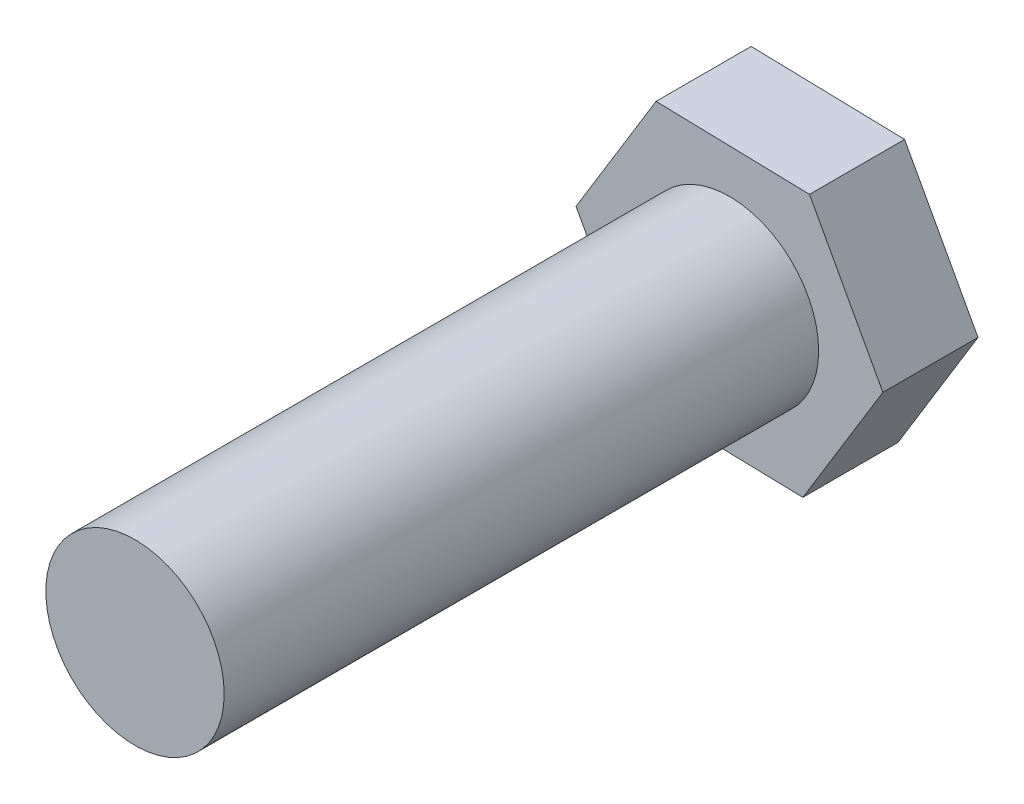
SolidWorks part; units mm, degrees
ref_plane "Front Plane" through (0, 0, 0) normal (0, 0, 1) x (1, 0, 0)
ref_plane "Top Plane" through (0, 0, 0) normal (0, 1, 0) x (1, 0, 0)
ref_plane "Right Plane" through (0, 0, 0) normal (1, 0, 0) x (0, 0, -1)
sketch "Sketch1" plane through (0, 0, 0) normal (0, 0, 1) x (1, 0, 0)
  line L1 (4.2749, 6.9946) -> (-3.9201, 7.1995)
  line L2 (-3.9201, 7.1995) -> (-8.195, 0.2049)
  line L3 (-8.195, 0.2049) -> (-4.2749, -6.9946)
  line L4 (-4.2749, -6.9946) -> (3.9201, -7.1995)
  line L5 (3.9201, -7.1995) -> (8.195, -0.2049)
  line L6 (8.195, -0.2049) -> (4.2749, 6.9946)
  circle A1 centre (0, 0) radius 7.0993 construction
extrude "Extrude1" add sketch "Sketch1" along normal blind 36.83
sketch "Sketch2" plane through (0, 0, 36.83) normal (0, 0, 1) x (1, 0, 0)
  circle A0 centre (0, 0) radius 4.7625
extrude "Extrude2" cut sketch "Sketch2" against normal blind 31.75 flip side to cut
